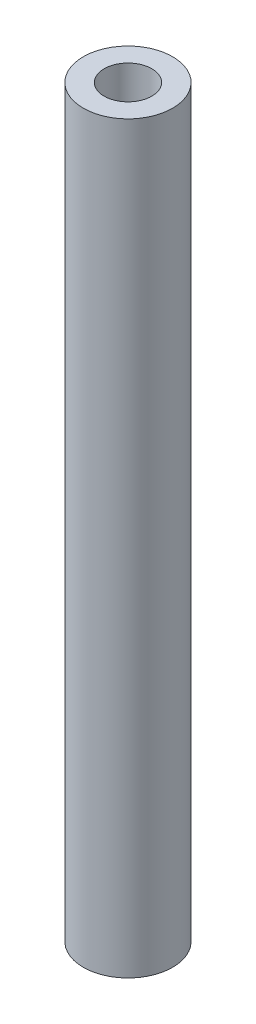
SolidWorks part; units mm, degrees
material "6061-T6 (SS)"
ref_plane "Front Plane" through (0, 0, 0) normal (0, 0, 1) x (1, 0, 0)
ref_plane "Top Plane" through (0, 0, 0) normal (0, 1, 0) x (1, 0, 0)
ref_plane "Right Plane" through (0, 0, 0) normal (1, 0, 0) x (0, 0, -1)
sketch "Sketch1" plane through (0, 0, 0) normal (0, 1, 0) x (1, 0, 0)
  circle A0 centre (0, 0) radius 3
  circle A1 centre (0, 0) radius 1.6
  dimension "D1" = 3.2
  dimension "D2" = 6
extrude "Boss-Extrude1" add sketch "Sketch1" along normal blind 50
